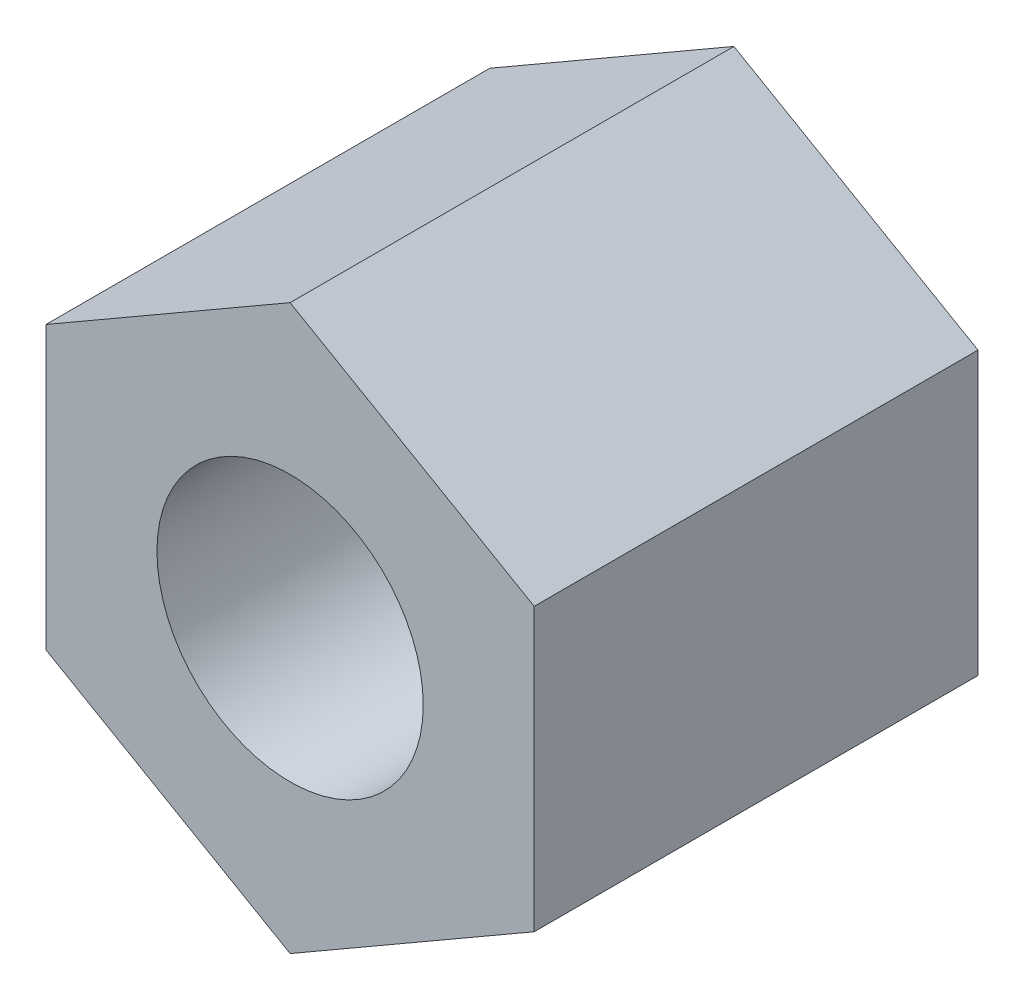
SolidWorks part; units mm, degrees
ref_plane "Спереди" through (0, 0, 0) normal (0, 0, 1) x (1, 0, 0)
ref_plane "Сверху" through (0, 0, 0) normal (0, 1, 0) x (1, 0, 0)
ref_plane "Справа" through (0, 0, 0) normal (1, 0, 0) x (0, 0, -1)
sketch "Эскиз1" plane through (0, 0, 0) normal (0, 0, 1) x (1, 0, 0)
  line L1 (0, -3.1754) -> (2.75, -1.5877)
  line L2 (2.75, -1.5877) -> (2.75, 1.5877)
  line L3 (2.75, 1.5877) -> (0, 3.1754)
  line L4 (0, 3.1754) -> (-2.75, 1.5877)
  line L5 (-2.75, 1.5877) -> (-2.75, -1.5877)
  line L6 (-2.75, -1.5877) -> (0, -3.1754)
  circle A0 centre (0, 0) radius 2.75 construction
  circle A1 centre (0, 0) radius 1.5
  dimension "D2" = 3
  dimension "D1" = 5.5
extrude "Бобышка-Вытянуть1" add sketch "Эскиз1" along normal blind 5
